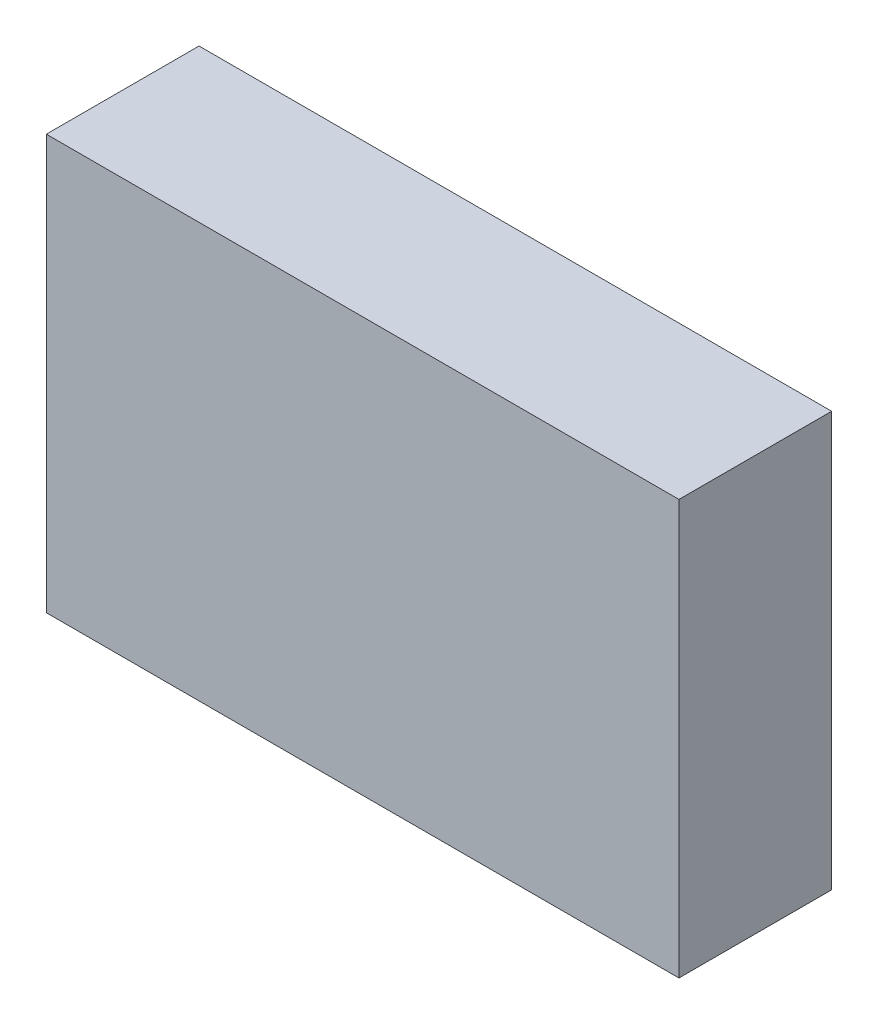
SolidWorks part; units mm, degrees
material "0.6010 (EN-GJL-100)"
ref_plane "Plan de face" through (0, 0, 0) normal (0, 0, 1) x (1, 0, 0)
ref_plane "Plan de dessus" through (0, 0, 0) normal (0, 1, 0) x (1, 0, 0)
ref_plane "Plan de droite" through (0, 0, 0) normal (1, 0, 0) x (0, 0, -1)
sketch "Esquisse1" plane through (0, 0, 0) normal (0, 0, 1) x (1, 0, 0)
  line L1 (0, 0) -> (290, 0)
  line L2 (0, 0) -> (0, 190)
  line L3 (0, 190) -> (290, 190)
  line L4 (290, 0) -> (290, 190)
  dimension "D1" = 290
  dimension "D2" = 190
extrude "Boss.-Extru.1" add sketch "Esquisse1" along normal blind 70
